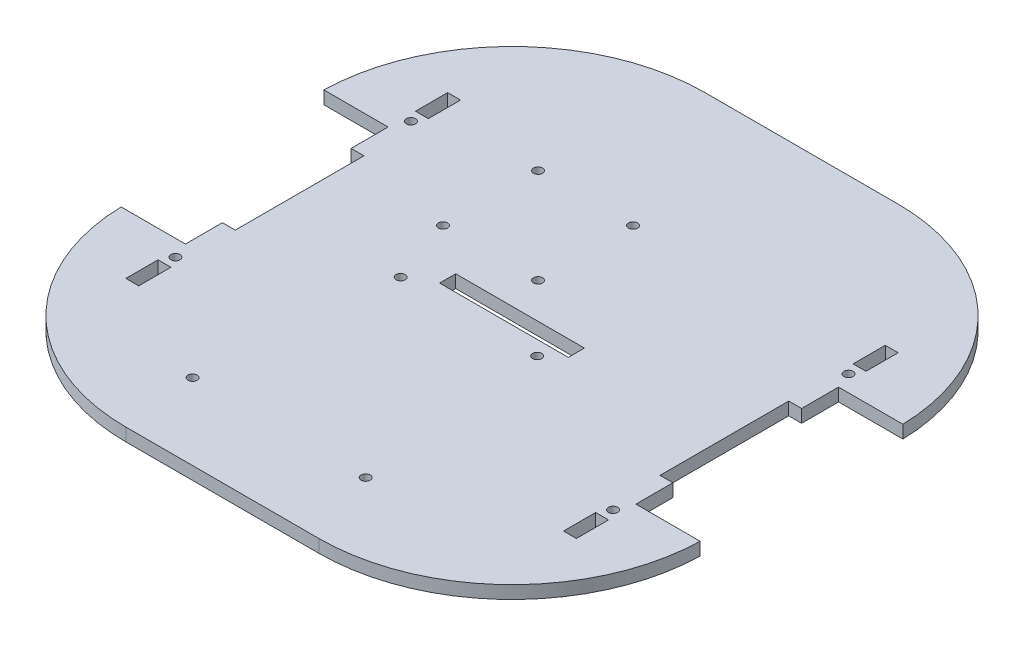
SolidWorks part; units mm, degrees
ref_plane "Front Plane" through (0, 0, 0) normal (0, 0, 1) x (1, 0, 0)
ref_plane "Top Plane" through (0, 0, 0) normal (0, 1, 0) x (1, 0, 0)
ref_plane "Right Plane" through (0, 0, 0) normal (1, 0, 0) x (0, 0, -1)
sketch "Sketch1" plane through (0, 0, 0) normal (0, 1, 0) x (1, 0, 0)
  line L1 (0, 0) -> (228.6, 0)
  line L2 (0, 0) -> (0, 228.6)
  line L3 (0, 228.6) -> (228.6, 228.6)
  line L4 (228.6, 0) -> (228.6, 228.6)
  dimension "D1" = 228.6
  dimension "D2" = 228.6
extrude "Boss-Extrude1" add sketch "Sketch1" along normal blind 5.08
sketch "Sketch2" plane through (0, 5.08, 0) normal (0, 1, 0) x (1, 0, 0)
  line L0 (0, 228.6) -> (0, 0) construction
  line L1 (0, 154.3) -> (25.4, 154.3)
  line L2 (0, 154.3) -> (0, 74.3)
  line L3 (0, 74.3) -> (25.4, 74.3)
  line L4 (25.4, 154.3) -> (25.4, 74.3)
  line L5 (25.4, 154.3) -> (25.4, 228.6) construction
  line L6 (228.6, 228.6) -> (0, 228.6) construction
  line L7 (25.4, 74.3) -> (25.4, 0) construction
  line L8 (0, 0) -> (228.6, 0) construction
  dimension "D1" = 80
  dimension "D2" = 25.4
extrude "Cut-Extrude1" cut sketch "Sketch2" against normal up to next (5.08 mm away)
ref_plane "Plane1" through (114.3, 0, 0) normal (-1, 0, 0) x (0, 0, 1)
mirror "Mirror1" about plane through (114.3, 0, 0) normal (-1, 0, 0) of "Cut-Extrude1"
sketch "Sketch3" plane through (0, 0, 0) normal (0, -1, 0) x (1, 0, 0)
  line L24 (30.48, -177.8) -> (30.48, -165.1) construction
  line L25 (30.48, -165.1) -> (25.4, -165.1) construction
  line L26 (25.4, -165.1) -> (25.4, -177.8) construction
  line L27 (25.4, -177.8) -> (30.48, -177.8) construction
  line L28 (30.48, -139.7) -> (30.48, -88.9) construction
  line L29 (30.48, -88.9) -> (25.4, -88.9) construction
  line L30 (25.4, -88.9) -> (25.4, -139.7) construction
  line L31 (25.4, -139.7) -> (30.48, -139.7) construction
  line L32 (30.48, -63.5) -> (25.4, -63.5) construction
  line L33 (25.4, -63.5) -> (25.4, -50.8) construction
  line L34 (25.4, -50.8) -> (30.48, -50.8) construction
  line L35 (30.48, -50.8) -> (30.48, -63.5) construction
  line L36 (30.48, -177.8) -> (30.48, -165.1)
  line L37 (30.48, -165.1) -> (25.4, -165.1)
  line L38 (25.4, -165.1) -> (25.4, -177.8)
  line L39 (25.4, -177.8) -> (30.48, -177.8)
  line L40 (30.48, -139.7) -> (30.48, -88.9)
  line L41 (30.48, -88.9) -> (25.4, -88.9)
  line L42 (25.4, -88.9) -> (25.4, -139.7)
  line L43 (25.4, -139.7) -> (30.48, -139.7)
  line L44 (30.48, -63.5) -> (25.4, -63.5)
  line L45 (25.4, -63.5) -> (25.4, -50.8)
  line L46 (25.4, -50.8) -> (30.48, -50.8)
  line L47 (30.48, -50.8) -> (30.48, -63.5)
extrude "Cut-Extrude2" cut sketch "Sketch3" against normal up to next (5.08 mm away)
mirror "Mirror2" about plane through (114.3, 0, 0) normal (-1, 0, 0) of "Cut-Extrude2"
sketch "Sketch5" plane through (0, 0, 0) normal (0, -1, 0) x (1, 0, 0)
  line L0 (0, -74.3) -> (0, 0) construction
  line L2 (0, 0) -> (228.6, 0) construction
  line L5 (0, -76.2) -> (0, 0)
  line L6 (0, 0) -> (76.2, 0)
  arc A0 (0, -76.2) -> (76.2, 0) centre (76.2, -76.2) cw
  dimension "D1" = 76.2
extrude "Cut-Extrude4" cut sketch "Sketch5" against normal up to next (5.08 mm away)
mirror "Mirror3" about plane through (114.3, 0, 0) normal (-1, 0, 0) of "Cut-Extrude4"
ref_plane "Plane2" through (0, 0, -114.3) normal (0, 0, 1) x (1, 0, 0)
mirror "Mirror4" about plane through (0, 0, -114.3) normal (0, 0, 1) of "Mirror3", "Cut-Extrude4"
sketch "Sketch7" plane through (0, 5.08, 0) normal (0, 1, 0) x (1, 0, 0)
  line L0 (88.9, 114.3) -> (30.48, 114.3) construction
  line L9 (88.9, 117.475) -> (139.7, 117.475)
  line L10 (88.9, 117.475) -> (88.9, 111.125)
  line L11 (88.9, 111.125) -> (139.7, 111.125)
  line L12 (139.7, 117.475) -> (139.7, 111.125)
  line L19 (30.48, 88.9) -> (30.48, 139.7) construction
  line L20 (139.7, 114.3) -> (198.12, 114.3) construction
  line L21 (198.12, 88.9) -> (198.12, 139.7) construction
  dimension "D1" = 50.8
  dimension "D4" = 6.35
extrude "Cut-Extrude6" cut sketch "Sketch7" against normal up to next
sketch "Sketch9" plane through (0, 5.08, 0) normal (0, 1, 0) x (1, 0, 0)
  circle A0 centre (69.9115, 168.9644) radius 1.5508 construction
  circle A1 centre (107.4115, 168.9644) radius 1.5508 construction
  circle A2 centre (69.9115, 131.4644) radius 1.5508 construction
  circle A3 centre (107.4115, 131.4644) radius 1.5508 construction
  circle A4 centre (69.9115, 168.9644) radius 1.5508
  circle A5 centre (107.4115, 168.9644) radius 1.5508
  circle A6 centre (69.9115, 131.4644) radius 1.5508
  circle A7 centre (107.4115, 131.4644) radius 1.5508
hole_wizard "M3 Clearance Hole1" positions "Sketch12" profile "Sketch13" hole size "M3" standard "ISO" end condition up to next
sketch "Sketch12" plane through (0, 5.08, 0) normal (0, 1, 0) x (1, 0, 0)
  point P0 (107.4115, 131.4644)
  point P3 (107.4115, 168.9644)
  point P6 (69.9115, 131.4644)
  point P9 (69.9115, 168.9644)
sketch "Sketch13" plane through (107.4115, 5.08, -131.4644) normal (1, 0, 0) x (0, 0, 1)
  line L0 (0, 0) -> (0, 5.08)
  line L1 (0, 5.08) -> (1.8, 5.08)
  line L2 (1.8, 5.08) -> (1.8, 0)
  line L5 (1.8, 0) -> (0, 0)
  line L11 (0, -6.35) -> (0, 107.95) construction
  dimension "Thru Hole Dia." = 3.6
  dimension "Thru Hole Depth" = 5.08
sketch "Sketch14" plane through (0, 5.08, 0) normal (0, 1, 0) x (1, 0, 0)
  circle A0 centre (72.4965, 30.0462) radius 1.8 construction
  circle A1 centre (133.0865, 105.4462) radius 1.8 construction
  circle A2 centre (79.1965, 105.4462) radius 1.8 construction
  circle A3 centre (140.7965, 30.0462) radius 1.8 construction
  circle A4 centre (72.4965, 30.0462) radius 1.8 construction
  circle A5 centre (133.0865, 105.4462) radius 1.8 construction
  circle A6 centre (79.1965, 105.4462) radius 1.8 construction
  circle A7 centre (140.7965, 30.0462) radius 1.8 construction
hole_wizard "M3 Clearance Hole2" positions "Sketch15" profile "Sketch16" hole size "M3" standard "ISO" end condition up to next
sketch "Sketch15" plane through (0, 5.08, 0) normal (0, 1, 0) x (1, 0, 0)
  point P0 (72.4965, 30.0462)
  point P3 (140.7965, 30.0462)
  point P6 (79.1965, 105.4462)
  point P9 (133.0865, 105.4462)
sketch "Sketch16" plane through (72.4965, 5.08, -30.0462) normal (1, 0, 0) x (0, 0, 1)
  line L0 (0, 0) -> (0, 5.08)
  line L1 (0, 5.08) -> (1.8, 5.08)
  line L2 (1.8, 5.08) -> (1.8, 0)
  line L5 (1.8, 0) -> (0, 0)
  line L11 (0, -6.35) -> (0, 107.95) construction
  dimension "Thru Hole Dia." = 3.6
  dimension "Thru Hole Depth" = 5.08
sketch "Sketch19" plane through (0, 0, 0) normal (0, -1, 0) x (1, 0, 0)
  line L0 (200.66, -66.04) -> (200.66, -63.5) construction
  line L2 (203.2, -63.5) -> (198.12, -63.5) construction
  circle A0 centre (200.66, -67.84) radius 1.8
  dimension "D1" = 3.6
  dimension "D2" = 2.54
extrude "Cut-Extrude7" cut sketch "Sketch19" against normal up to next (5.08 mm away)
mirror "Mirror5" about plane through (0, 0, -114.3) normal (0, 0, 1) of "Cut-Extrude7"
mirror "Mirror6" about plane through (114.3, 0, 0) normal (-1, 0, 0) of "Mirror5", "Cut-Extrude7"
equation "\"Foamcore\"= 0.2in"
equation "\"MDF\"= 0.2in"
equation "\"D1@Boss-Extrude1\"=\"MDF\""
equation "\"TubeR\"= 0.8in"
equation "\"NutD\"= 0.2145in"
equation "\"NutH\"= 0.0915in"
equation "\"MountScrewL\"= 0.3in"
equation "\"MountScrewD\"= 3.6mm"
equation "\"D1@Sketch19\"=\"MountScrewD\""
